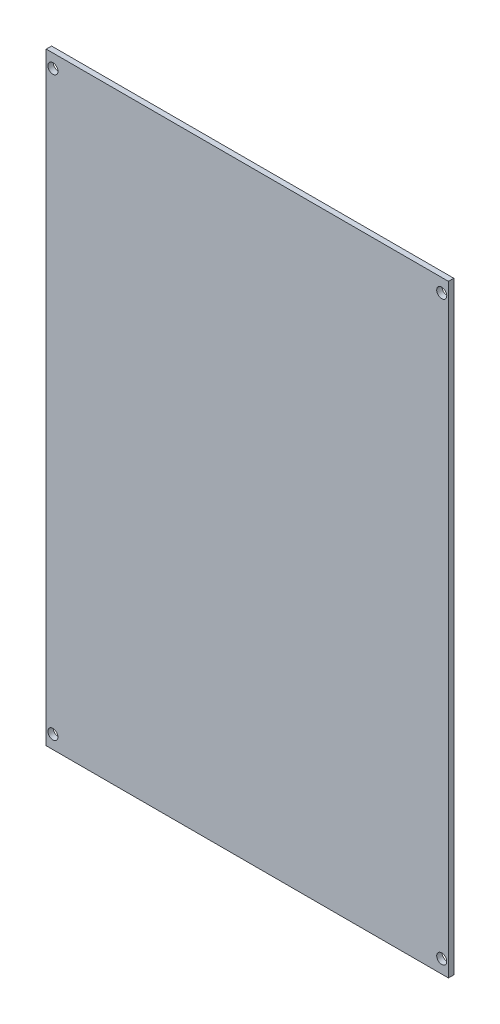
SolidWorks part; units mm, degrees
ref_plane "Płaszczyzna przednia" through (0, 0, 0) normal (0, 0, 1) x (1, 0, 0)
ref_plane "Płaszczyzna górna" through (0, 0, 0) normal (0, 1, 0) x (1, 0, 0)
ref_plane "Płaszczyzna prawa" through (0, 0, 0) normal (1, 0, 0) x (0, 0, -1)
sketch "Sketch1" plane through (0, 0, 0) normal (0, 0, 1) x (1, 0, 0)
  line L1 (60, -90) -> (-60, -90)
  line L2 (60, -90) -> (60, 90)
  line L3 (60, 90) -> (-60, 90)
  line L4 (-60, -90) -> (-60, 90)
  line L5 (60, -90) -> (-60, 90) construction
  line L6 (60, 90) -> (-60, -90) construction
  point P0 (0, 0)
  dimension "D1" = 120
  dimension "D2" = 180
extrude "Boss-Extrude1" add sketch "Sketch1" along normal blind 1.6
sketch "Sketch2" plane through (0, 0, 0) normal (0, 0, 1) x (1, 0, 0)
  line L0 (-60, -90) -> (60, -90) construction
  line L1 (-58, -86) -> (58, -86) construction
  line L2 (-58, -86) -> (-58, 86) construction
  line L3 (-58, 86) -> (58, 86) construction
  line L4 (58, -86) -> (58, 86) construction
  line L5 (-58, -86) -> (58, 86) construction
  line L6 (-58, 86) -> (58, -86) construction
  line L8 (-60, 90) -> (-60, -90) construction
  circle A0 centre (-58, 86) radius 1.5
  circle A1 centre (58, 86) radius 1.5
  circle A2 centre (58, -86) radius 1.5
  circle A3 centre (-58, -86) radius 1.5
  point P0 (0, 0)
  dimension "D3" = 3
  dimension "D1" = 4
  dimension "D2" = 2
extrude "Cut-Extrude2" cut sketch "Sketch2" along normal through all both and the other way through all
